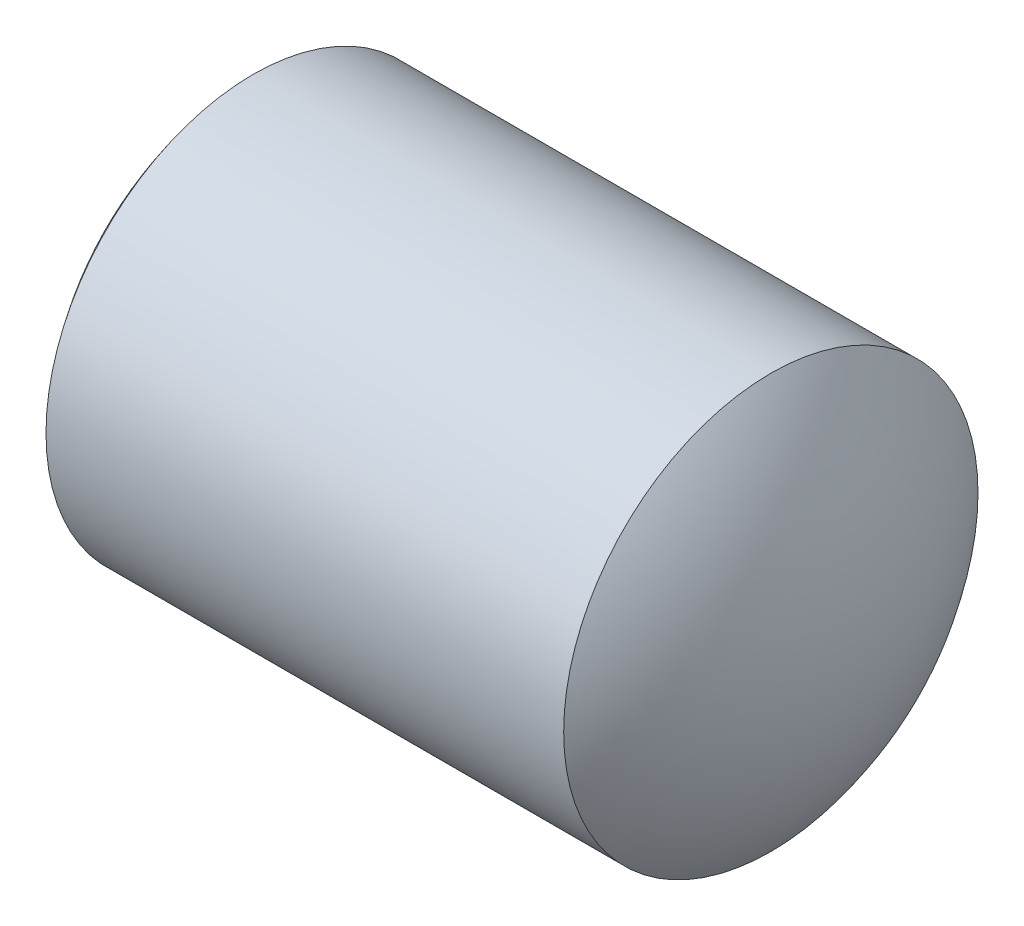
SolidWorks part; units mm, degrees
ref_plane "前视基准面" through (0, 0, 0) normal (0, 0, 1) x (1, 0, 0)
ref_plane "上视基准面" through (0, 0, 0) normal (0, 1, 0) x (1, 0, 0)
ref_plane "右视基准面" through (0, 0, 0) normal (1, 0, 0) x (0, 0, -1)
sketch "草图1" plane through (0, 0, 0) normal (0, 0, 1) x (1, 0, 0)
  line L0 (-3.1229, 2.4995) -> (-3.1229, 0) construction
  line L1 (-3.1229, 2.4995) -> (3.1229, 2.4995)
  line L2 (-4, 0) -> (4, 0)
  line L3 (3.1229, 2.4995) -> (3.1229, 0) construction
  line L4 (-4.636, 0) -> (5.1194, 0) construction
  arc A0 (-3.1229, 2.4995) -> (-4, 0) centre (0, 0) ccw
  circle A1 centre (0, 0) radius 2.5 construction
  arc A3 (4, 0) -> (3.1229, 2.4995) centre (0, 0) ccw
  dimension "D2" = 8
revolve "旋转1" add sketch "草图1" angle 360 about L4
